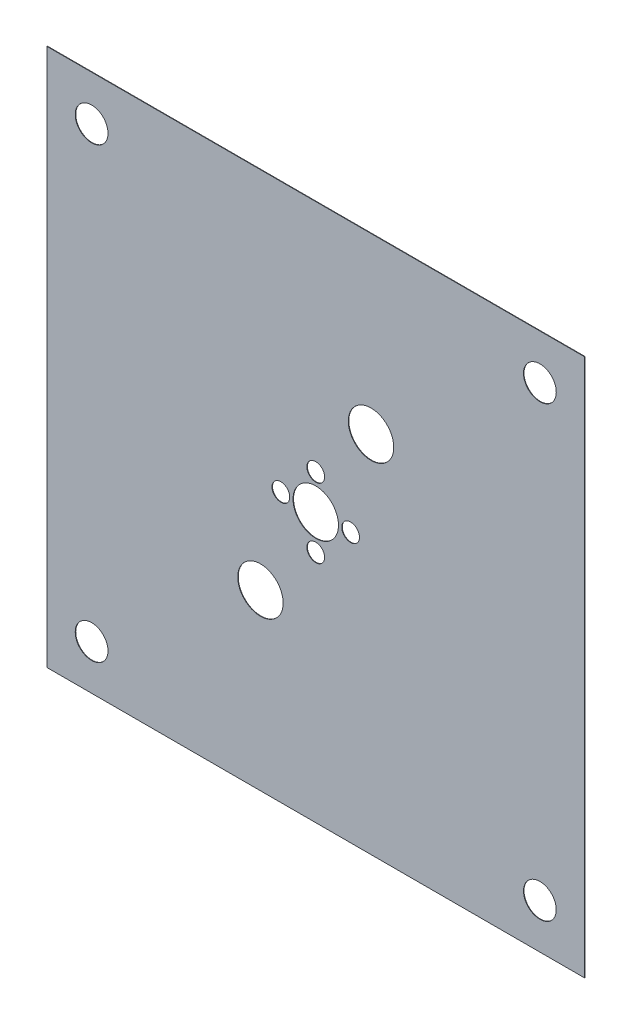
SolidWorks part; units mm, degrees
ref_plane "Front" through (0, 0, 0) normal (0, 0, 1) x (1, 0, 0)
ref_plane "Top" through (0, 0, 0) normal (0, 1, 0) x (1, 0, 0)
ref_plane "Right" through (0, 0, 0) normal (1, 0, 0) x (0, 0, -1)
sketch "Sketch1" plane through (0, 0, 0) normal (0, 0, 1) x (1, 0, 0)
  line L0 (-1080, 0) -> (1080, 0) construction
  line L1 (-1080, 1080) -> (1080, 1080)
  line L2 (-1080, 1080) -> (-1080, -1080)
  line L3 (-1080, -1080) -> (1080, -1080)
  line L4 (1080, 1080) -> (1080, -1080)
  line L5 (-1080, 1080) -> (1080, -1080) construction
  line L6 (-1080, -1080) -> (1080, 1080) construction
  line L7 (0, 1080) -> (0, -1080) construction
  circle A0 centre (0, 0) radius 91.2
  circle A1 centre (0, 140) radius 35.6375
  circle A2 centre (222, 382) radius 91.2
  circle A3 centre (-222, -382) radius 91.2
  circle A4 centre (-900, 900) radius 65.8
  circle A5 centre (900, -900) radius 65.8
  circle A6 centre (900, 900) radius 65.8
  circle A7 centre (-900, -900) radius 65.8
  circle A8 centre (0, -140) radius 35.6375
  circle A9 centre (140, 0) radius 35.6375
  circle A10 centre (-140, 0) radius 35.6375
  point P0 (0, 0)
  dimension "D3" = 182.4
  dimension "D4" = 71.275
  dimension "D6" = 182.4
  dimension "D9" = 182.4
  dimension "D12" = 131.6
  dimension "D1" = 2160
  dimension "D2" = 2160
  dimension "D5" = 140
  dimension "D7" = 222
  dimension "D8" = 382
  dimension "D10" = 222
  dimension "D11" = 382
  dimension "D13" = 900
extrude "Boss-Extrude1" add sketch "Sketch1" along normal blind 2
